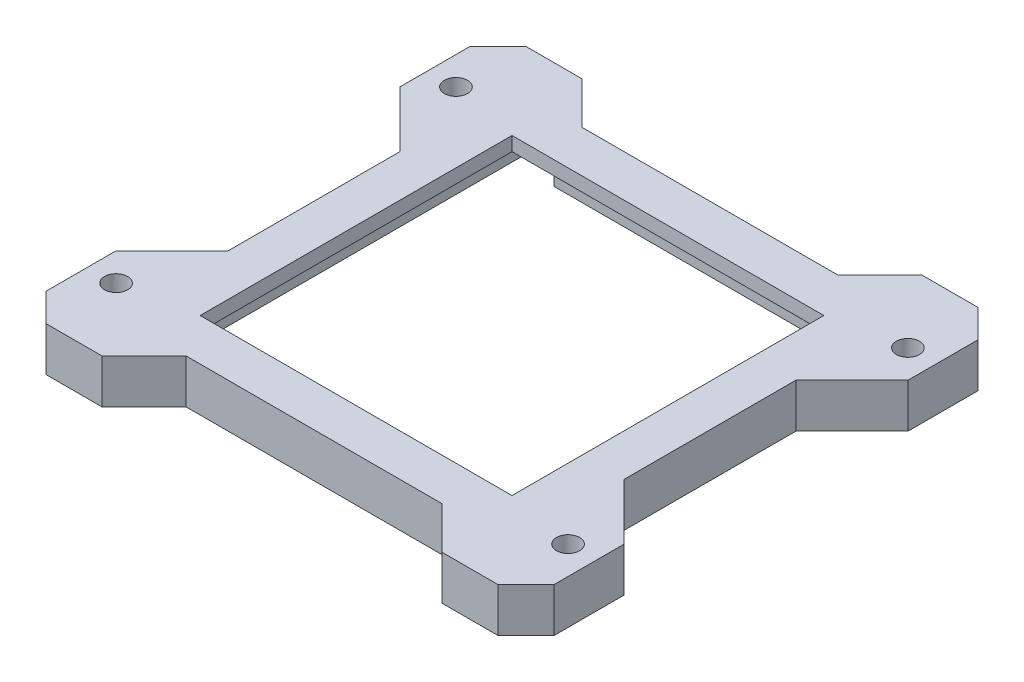
SolidWorks part; units mm, degrees
ref_plane "Front Plane" through (0, 0, 0) normal (0, 0, 1) x (1, 0, 0)
ref_plane "Top Plane" through (0, 0, 0) normal (0, 1, 0) x (1, 0, 0)
ref_plane "Right Plane" through (0, 0, 0) normal (1, 0, 0) x (0, 0, -1)
sketch "Sketch1" plane through (0, 0, 0) normal (0, 1, 0) x (1, 0, 0)
  line L0 (-28.25, 12.25) -> (-36.25, 20.25)
  line L1 (-25.25, 25.25) -> (25.25, 25.25)
  line L2 (-25.25, 25.25) -> (-25.25, -25.25)
  line L3 (-25.25, -25.25) -> (25.25, -25.25)
  line L4 (25.25, 25.25) -> (25.25, -25.25)
  line L5 (-25.25, 25.25) -> (25.25, -25.25) construction
  line L6 (-25.25, -25.25) -> (25.25, 25.25) construction
  line L7 (-28.25, 28.25) -> (28.25, 28.25)
  line L8 (-28.25, 28.25) -> (-28.25, -28.25)
  line L9 (-28.25, -28.25) -> (28.25, -28.25)
  line L10 (28.25, 28.25) -> (28.25, -28.25)
  line L11 (-28.25, 28.25) -> (28.25, -28.25) construction
  line L12 (-28.25, -28.25) -> (28.25, 28.25) construction
  line L13 (-36.25, 20.25) -> (-36.25, 30.25)
  line L14 (-36.25, 30.25) -> (-32.25, 34.25)
  line L15 (-32.25, 34.25) -> (-24.25, 34.25)
  line L16 (-24.25, 34.25) -> (-18.25, 28.25)
  line L17 (-55, 0) -> (55, 0) construction
  line L18 (-28.25, -12.25) -> (-36.25, -20.25)
  line L19 (-24.25, -34.25) -> (-18.25, -28.25)
  line L20 (-32.25, -34.25) -> (-24.25, -34.25)
  line L21 (-36.25, -30.25) -> (-32.25, -34.25)
  line L22 (-36.25, -20.25) -> (-36.25, -30.25)
  line L23 (0, -55) -> (0, 55) construction
  line L24 (32.25, -34.25) -> (24.25, -34.25)
  line L25 (24.25, -34.25) -> (18.25, -28.25)
  line L26 (28.25, -12.25) -> (36.25, -20.25)
  line L27 (36.25, -20.25) -> (36.25, -30.25)
  line L28 (36.25, -30.25) -> (32.25, -34.25)
  line L29 (24.25, 34.25) -> (18.25, 28.25)
  line L30 (32.25, 34.25) -> (24.25, 34.25)
  line L31 (36.25, 30.25) -> (32.25, 34.25)
  line L32 (36.25, 20.25) -> (36.25, 30.25)
  line L33 (28.25, 12.25) -> (36.25, 20.25)
  circle A0 centre (-32.25, 24.25) radius 1.65
  circle A1 centre (-32.25, -24.25) radius 1.65
  circle A2 centre (32.25, -24.25) radius 1.65
  circle A3 centre (32.25, 24.25) radius 1.65
  point P0 (0, 0)
  point P5 (0, 0)
  dimension "D11" = 3.3
  dimension "D12" = 4
  dimension "D1" = 50.5
  dimension "D2" = 50.5
  dimension "D3" = 56.5
  dimension "D4" = 6
  dimension "D5" = 8
  dimension "D6" = 4
  dimension "D7" = 8
  dimension "D8" = 4
  dimension "D9" = 4
  dimension "D10" = 45
  dimension "D13" = 4
extrude "Boss-Extrude1" add sketch "Sketch1" along normal blind 8.6 contours L10 L7 L8 L9 L1 L4 L3 L2 | L18 L22 L21 L20 L19 L9 L8 A1 | L28 L27 L26 L10 L9 L25 L24 A2 | L10 L33 L32 L31 L30 L29 L7 A3 | L16 L15 L14 L13 L0 L8 L7 A0
sketch "Sketch2" plane through (0, 0, 0) normal (0, 1, 0) x (1, 0, 0)
  line L1 (-25.25, 25.25) -> (25.25, 25.25)
  line L2 (-25.25, 25.25) -> (-25.25, -25.25)
  line L3 (-25.25, -25.25) -> (25.25, -25.25)
  line L4 (25.25, 25.25) -> (25.25, -25.25)
  line L5 (-25.25, 25.25) -> (25.25, -25.25) construction
  line L6 (-25.25, -25.25) -> (25.25, 25.25) construction
  line L7 (-22.25, 22.25) -> (22.25, 22.25)
  line L8 (-22.25, 22.25) -> (-22.25, -22.25)
  line L9 (-22.25, -22.25) -> (22.25, -22.25)
  line L10 (22.25, 22.25) -> (22.25, -22.25)
  line L11 (-22.25, 22.25) -> (22.25, -22.25) construction
  line L12 (-22.25, -22.25) -> (22.25, 22.25) construction
  point P0 (0, 0)
  point P5 (0, 0)
  dimension "D1" = 50.5
  dimension "D2" = 50.5
  dimension "D3" = 44.5
  dimension "D4" = 44.5
extrude "Boss-Extrude2" add sketch "Sketch2" along normal blind 2
sketch "Sketch4" plane through (0, 0, 0) normal (0, 1, 0) x (1, 0, 0)
  line L1 (-25.25, 25.25) -> (25.25, 25.25)
  line L2 (-25.25, 25.25) -> (-25.25, -25.25)
  line L3 (-25.25, -25.25) -> (25.25, -25.25)
  line L4 (25.25, 25.25) -> (25.25, -25.25)
  line L5 (-25.25, 25.25) -> (25.25, -25.25) construction
  line L6 (-25.25, -25.25) -> (25.25, 25.25) construction
  line L7 (-22.25, 22.25) -> (22.25, 22.25)
  line L8 (-22.25, 22.25) -> (-22.25, -22.25)
  line L9 (-22.25, -22.25) -> (22.25, -22.25)
  line L10 (22.25, 22.25) -> (22.25, -22.25)
  line L11 (-22.25, 22.25) -> (22.25, -22.25) construction
  line L12 (-22.25, -22.25) -> (22.25, 22.25) construction
  point P0 (0, 0)
  point P5 (0, 0)
extrude "Boss-Extrude3" add sketch "Sketch4" along normal blind 2 from offset 6.6
sketch "Sketch5" plane through (0, 0, 0) normal (0, 1, 0) x (1, 0, 0)
  line L1 (-25.25, 19.8891) -> (-19.25, 19.8891)
  line L2 (-25.25, 19.8891) -> (-25.25, 37.8505)
  line L3 (-25.25, 37.8505) -> (-19.25, 37.8505)
  line L4 (-19.25, 19.8891) -> (-19.25, 37.8505)
  line L5 (19.25, 19.8891) -> (25.25, 19.8891)
  line L6 (19.25, 19.8891) -> (19.25, 37.8505)
  line L7 (19.25, 37.8505) -> (25.25, 37.8505)
  line L8 (25.25, 19.8891) -> (25.25, 37.8505)
  dimension "D1" = 6
  dimension "D2" = 6
  dimension "D3" = 25.25
  dimension "D4" = 25.25
extrude "Cut-Extrude1" cut sketch "Sketch5" along normal blind 4.6 from offset 2
sketch "Sketch6" plane through (0, 0, 0) normal (0, -1, 0) x (1, 0, 0)
  line L1 (-41.762, 39.56) -> (45.5585, 39.56)
  line L2 (-41.762, 39.56) -> (-41.762, -42.5972)
  line L3 (-41.762, -42.5972) -> (45.5585, -42.5972)
  line L4 (45.5585, 39.56) -> (45.5585, -42.5972)
extrude "Cut-Extrude2" cut sketch "Sketch6" against normal blind 2.3
